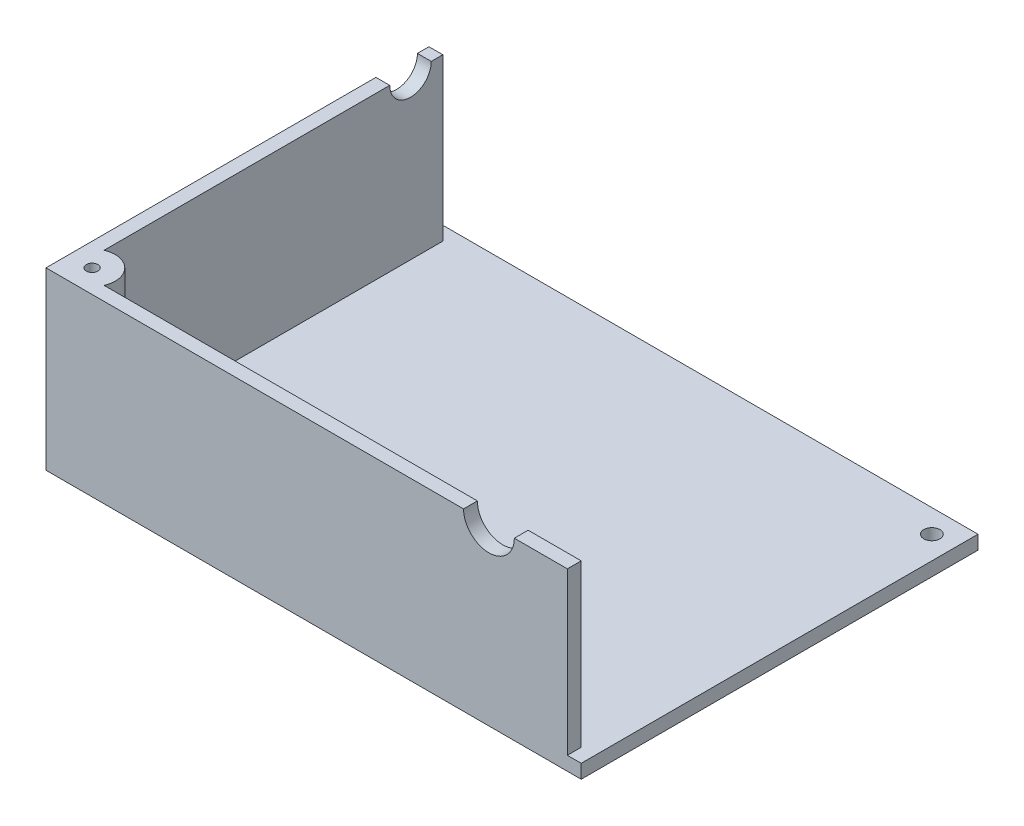
SolidWorks part; units mm, degrees
ref_plane "前视基准面" through (0, 0, 0) normal (0, 0, 1) x (1, 0, 0)
ref_plane "上视基准面" through (0, 0, 0) normal (0, 1, 0) x (1, 0, 0)
ref_plane "右视基准面" through (0, 0, 0) normal (1, 0, 0) x (0, 0, -1)
other "Configuration Table"
sketch "Sketch1" plane through (0, 0, 0) normal (0, 1, 0) x (1, 0, 0)
  line L1 (0, 0) -> (116, 0)
  line L2 (0, 0) -> (0, 86)
  line L3 (0, 86) -> (116, 86)
  line L4 (116, 0) -> (116, 86)
  dimension "D1" = 86
  dimension "D2" = 116
extrude "Boss-Extrude1" add sketch "Sketch1" along normal blind 3
sketch "Sketch2" plane through (0, 3, 0) normal (0, 1, 0) x (1, 0, 0)
  line L1 (0, 0) -> (113, 0)
  line L2 (0, 0) -> (0, 3)
  line L3 (0, 3) -> (113, 3)
  line L4 (113, 0) -> (113, 3)
  dimension "D1" = 113
  dimension "D2" = 3
extrude "Boss-Extrude2" add sketch "Sketch2" along normal blind 35
sketch "Sketch3" plane through (0, 3, 0) normal (0, 1, 0) x (1, 0, 0)
  line L0 (116, 86) -> (0, 86) construction
  line L1 (0, 3) -> (3, 3)
  line L2 (0, 3) -> (0, 83)
  line L3 (0, 83) -> (3, 83)
  line L4 (3, 3) -> (3, 83)
  dimension "D1" = 3
  dimension "D2" = 3
extrude "Boss-Extrude3" add sketch "Sketch3" along normal blind 35
sketch "Sketch4" plane through (0, 0, 0) normal (0, -1, 0) x (1, 0, 0)
  line L0 (116, 0) -> (116, -86) construction
  line L1 (116, -86) -> (0, -86) construction
  circle A0 centre (111, -81) radius 1.75
  dimension "D3" = 3.5
  dimension "D1" = 5
  dimension "D2" = 5
extrude "Cut-Extrude1" cut sketch "Sketch4" against normal blind 35
sketch "Sketch5" plane through (0, 38, 0) normal (0, 1, 0) x (1, 0, 0)
  line L0 (0, 0) -> (113, 0) construction
  line L1 (0, 83) -> (0, 0) construction
  circle A0 centre (5, 5) radius 5
  circle A1 centre (5, 5) radius 1.25
  dimension "D1" = 10
  dimension "D2" = 2.5
extrude "Boss-Extrude4" add sketch "Sketch5" against normal blind 10
sketch "Sketch6" plane through (0, 0, 0) normal (0, 0, 1) x (1, 0, 0)
  line L0 (0, 38) -> (113, 38) construction
  circle A0 centre (96, 38) radius 5.5
  dimension "D2" = 11
  dimension "D1" = 17
extrude "Cut-Extrude2" cut sketch "Sketch6" against normal blind 10
sketch "Sketch7" plane through (0, 0, 0) normal (-1, 0, 0) x (0, 0, 1)
  line L0 (-83, 38) -> (0, 38) construction
  circle A0 centre (-76, 38) radius 4.5
  dimension "D2" = 9
  dimension "D1" = 7
extrude "Cut-Extrude3" cut sketch "Sketch7" against normal blind 10
